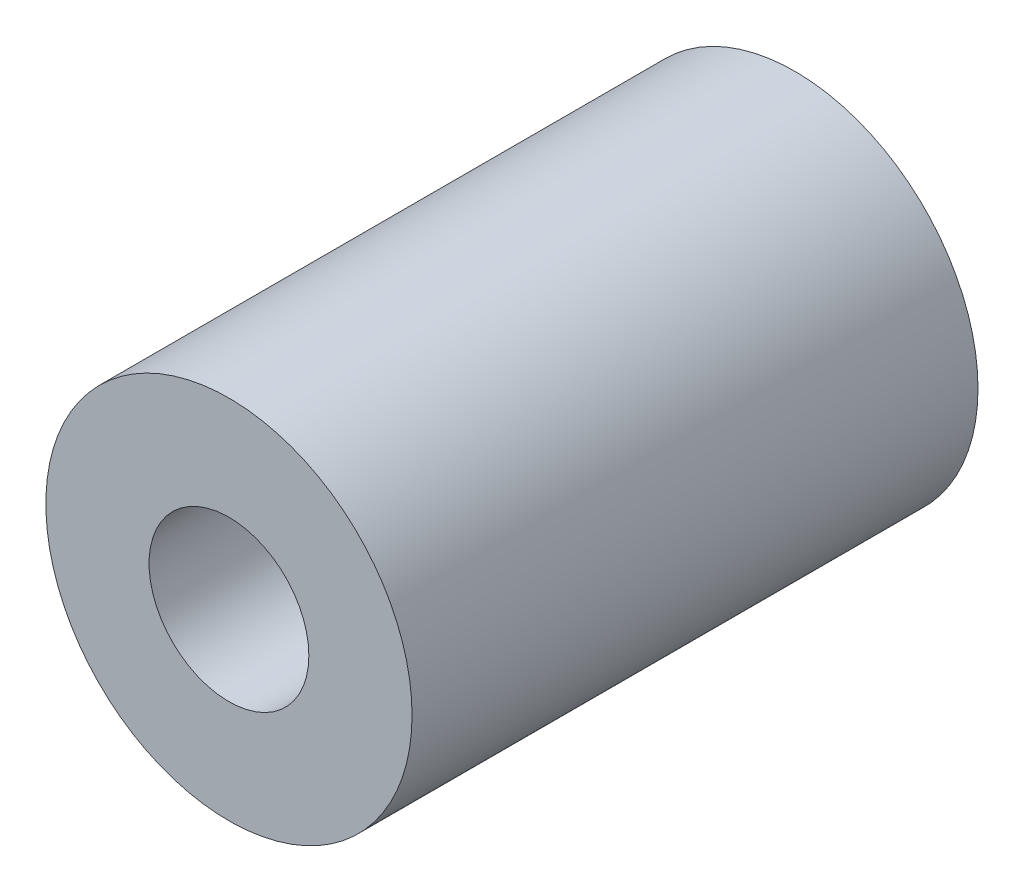
SolidWorks part; units mm, degrees
ref_plane "Front" through (0, 0, 0) normal (0, 0, 1) x (1, 0, 0)
ref_plane "Top" through (0, 0, 0) normal (0, 1, 0) x (1, 0, 0)
ref_plane "Right" through (0, 0, 0) normal (1, 0, 0) x (0, 0, -1)
sketch "Sketch2" plane through (0, 0, 0) normal (0, 0, 1) x (1, 0, 0)
  circle A0 centre (0, 0) radius 27.5
  circle A1 centre (0, 0) radius 12
  dimension "D1" = 24
  dimension "D2" = 55
extrude "Boss-Extrude1" add sketch "Sketch2" along normal blind 85
sketch "Sketch3" plane through (0, 0, 0) normal (1, 0, 0) x (0, 0, -1)
  line L0 (0, 0) -> (-112.5851, 0) construction
sketch "Sketch4" plane through (0, 0, 0) normal (1, 0, 0) x (0, 0, -1)
  point P0 (-85, 27.5)
